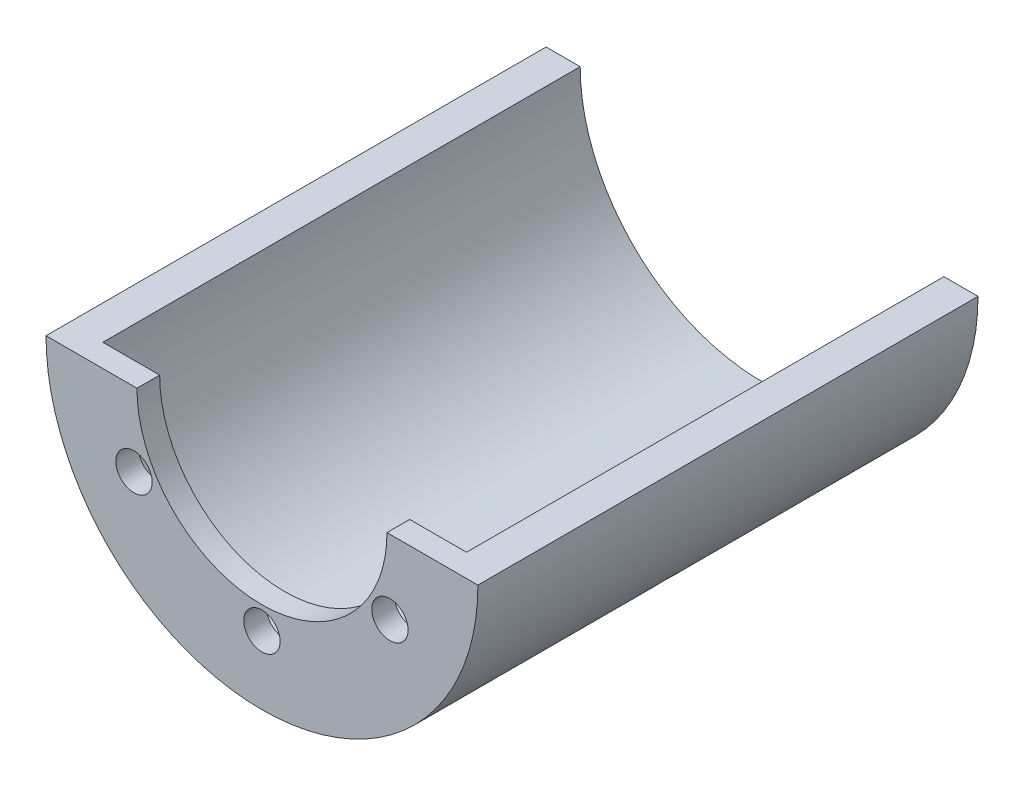
SolidWorks part; units mm, degrees
material "Ti-6Al-4VSolution treated and aged (SS)"
ref_plane "Front Plane" through (0, 0, 0) normal (0, 0, 1) x (1, 0, 0)
ref_plane "Top Plane" through (0, 0, 0) normal (0, 1, 0) x (1, 0, 0)
ref_plane "Right Plane" through (0, 0, 0) normal (1, 0, 0) x (0, 0, -1)
sketch "Sketch1" plane through (0, 0, 0) normal (0, 0, 1) x (1, 0, 0)
  circle A0 centre (0, 0) radius 9.5
  dimension "D1" = 19
extrude "Boss-Extrude1" add sketch "Sketch1" along normal blind 21
sketch "Sketch2" plane through (0, 0, 21) normal (0, 0, 1) x (1, 0, 0)
  circle A0 centre (0, 0) radius 8
  dimension "D1" = 16
extrude "Cut-Extrude1" cut sketch "Sketch2" against normal through all
sketch "Sketch4" plane through (0, 0, 21) normal (0, 0, 1) x (1, 0, 0)
  line L0 (-11.688, 0) -> (14.7909, 0) construction
  line L1 (-9.5, 0) -> (9.5, 0)
  line L2 (-9.5, 0) -> (-9.5, 9.5)
  line L3 (-9.5, 9.5) -> (9.5, 9.5)
  line L4 (9.5, 0) -> (9.5, 9.5)
  line L5 (9.5, 0) -> (9.5, 6.2077) construction
  line L6 (-9.5, 0) -> (-9.5, 0.9729) construction
  line L7 (0, 9.5) -> (7.7472, 9.5) construction
  circle A0 centre (0, 0) radius 9.5 construction
extrude "Cut-Extrude2" cut sketch "Sketch4" against normal through all
ref_plane "Plane1" through (0, -9.75, 0) normal (0, 1, 0) x (1, 0, 0)
sketch "Sketch5" plane through (0, 0, 21) normal (0, 0, 1) x (1, 0, 0)
  line L0 (-9.5, 0) -> (9.5, 0)
  arc A0 (9.5, 0) -> (0, -9.5) centre (0, 0) cw
  arc A1 (-9.5, 0) -> (9.5, 0) centre (0, 0) ccw construction
  arc A2 (-9.5, 0) -> (9.5, 0) centre (0, 0) ccw
  line M3 (-8, 0) -> (-9.5, 0)
  arc M4 (-9.5, 0) -> (9.5, 0) centre (0, 0) ccw
  line M5 (9.5, 0) -> (8, 0)
  arc M6 (8, 0) -> (-8, 0) centre (0, 0) cw
extrude "Boss-Extrude3" add sketch "Sketch5" along normal blind 1 contours M6 M3 M4 M5 | L0 M6
sketch "Sketch7" plane through (0, -9.75, 0) normal (0, 1, 0) x (1, 0, 0)
  line L0 (0, 0) -> (0, -22) construction
  line L1 (9.5, 0) -> (-9.5, 0) construction
  line L2 (-9.5, -22) -> (9.5, -22) construction
  line L3 (0, -11) -> (-8.6294, -11) construction
  circle A0 centre (0, -11) radius 0.5
  circle A1 centre (0, 4) radius 0.5
  circle A2 centre (0, -26) radius 0.5
  dimension "D3" = 1
  dimension "D1" = 15
  dimension "D2" = 15
extrude "Cut-Extrude8" cut sketch "Sketch7" along normal blind 0.5
pattern_circular "CirPattern1" count 2 every 45 of "Cut-Extrude8"
sketch "Sketch8" plane through (0, 0, 22) normal (0, 0, 1) x (1, 0, 0)
  line L0 (9.5, 0) -> (-9.5, 0) construction
  circle A0 centre (0, 0) radius 5.5
  dimension "D1" = 11
extrude "Cut-Extrude9" cut sketch "Sketch8" against normal through all
sketch "Sketch9" plane through (0, 0, 21) normal (0, 0, -1) x (-1, 0, 0)
  line L0 (0, -5.5) -> (0, -7.5) construction
  arc A0 (-5.5, 0) -> (5.5, 0) centre (0, 0) ccw construction
  circle A1 centre (0, -6.5) radius 0.8
  arc A3 (-8, 0) -> (8, 0) centre (0, 0) ccw construction
  circle A4 centre (0, 0) radius 6.5 construction
  point P12 (0, -8)
  dimension "D1" = 1.6
  dimension "D2" = 1.5
extrude "Cut-Extrude10" cut sketch "Sketch9" against normal through all
pattern_circular "CirPattern2" count 6 over 360 about axis through (0, 0, 0) along (0, 0, 1) of "Cut-Extrude10"
